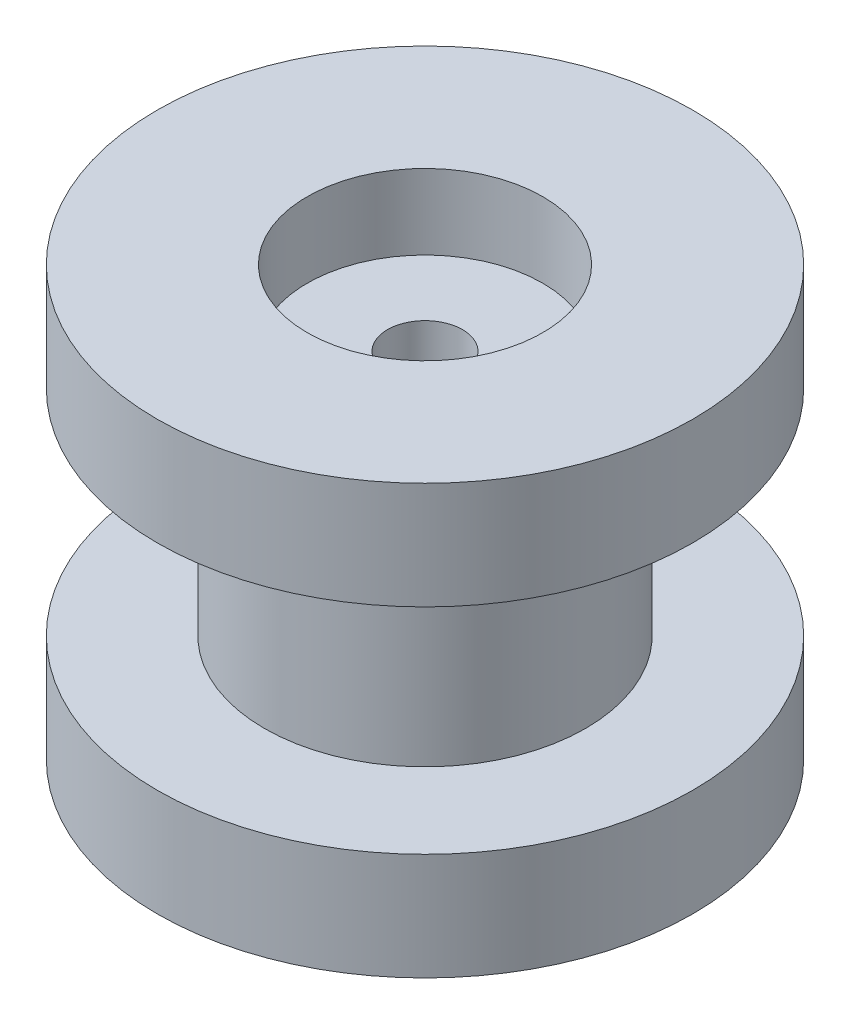
SolidWorks part; units mm, degrees
ref_plane "Front Plane" through (0, 0, 0) normal (0, 0, 1) x (1, 0, 0)
ref_plane "Top Plane" through (0, 0, 0) normal (0, 1, 0) x (1, 0, 0)
ref_plane "Right Plane" through (0, 0, 0) normal (1, 0, 0) x (0, 0, -1)
sketch "Sketch1" plane through (0, 0, 0) normal (0, 1, 0) x (1, 0, 0)
  circle A0 centre (0, 0) radius 12.5
extrude "Boss-Extrude1" add sketch "Sketch1" along normal blind 5 contours A0
sketch "Sketch2" plane through (0, 5, 0) normal (0, 1, 0) x (1, 0, 0)
  circle A0 centre (0, 0) radius 7.5
extrude "Boss-Extrude2" add sketch "Sketch2" along normal blind 5
mirror "Mirror6" about plane through (0, 10, 0) normal (0, 1, 0) of bodies 102
sketch "Sketch3" plane through (0, 20, 0) normal (0, 1, 0) x (1, 0, 0)
  circle A0 centre (0, 0) radius 5.5
extrude "Cut-Extrude1" cut sketch "Sketch3" against normal blind 3.5
sketch "Sketch5" plane through (0, 0, 0) normal (0, 1, 0) x (1, 0, 0)
sketch "Sketch6" plane through (0, 0, 0) normal (0, -1, 0) x (1, 0, 0)
  circle A0 centre (0, 0) radius 1.75
extrude "Cut-Extrude2" cut sketch "Sketch6" against normal through all
